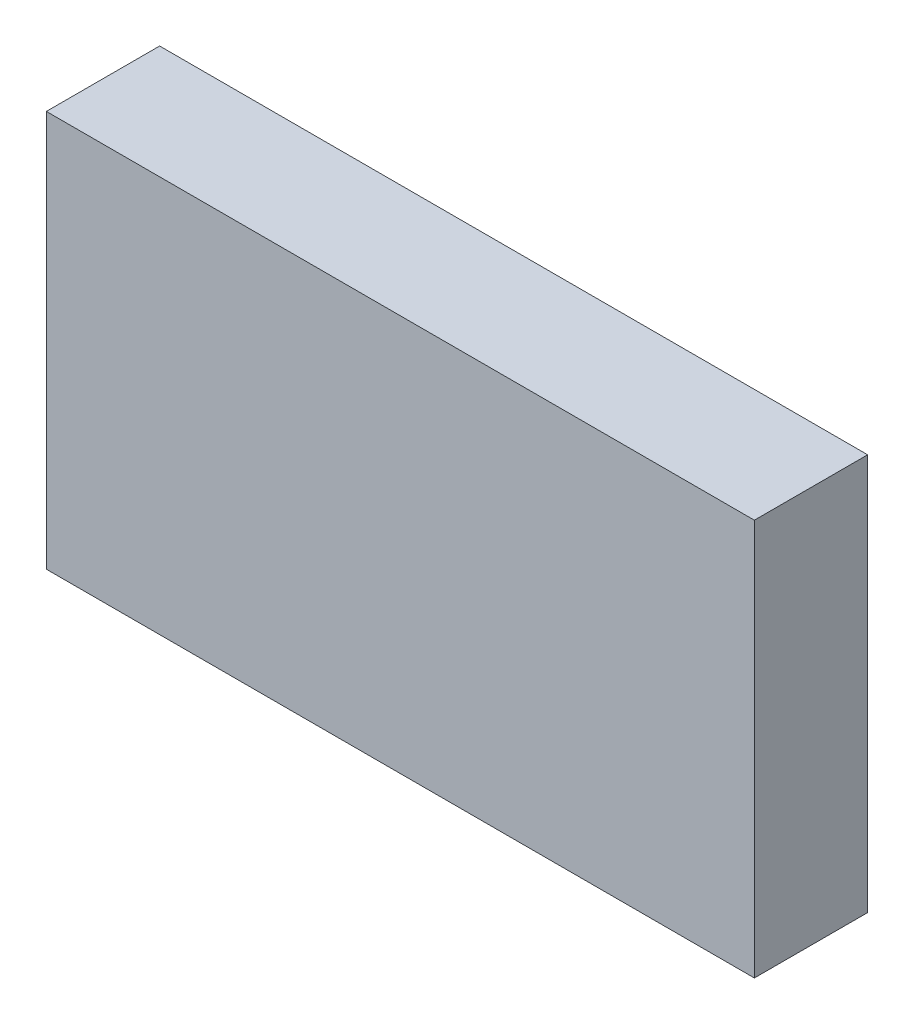
SolidWorks part; units mm, degrees
other "Target"
ref_plane "Front Plane" through (0, 0, 0) normal (0, 0, 1) x (1, 0, 0)
ref_plane "Top Plane" through (0, 0, 0) normal (0, 1, 0) x (1, 0, 0)
ref_plane "Right Plane" through (0, 0, 0) normal (1, 0, 0) x (0, 0, -1)
sketch "Sketch1" plane through (0, 0, 0) normal (0, 0, 1) x (1, 0, 0)
  line L1 (-76.2, -41.275) -> (76.2, -41.275)
  line L2 (-76.2, -41.275) -> (-76.2, 41.275)
  line L3 (-76.2, 41.275) -> (76.2, 41.275)
  line L4 (76.2, -41.275) -> (76.2, 41.275)
  line L5 (-76.2, -41.275) -> (76.2, 41.275) construction
  line L6 (-76.2, 41.275) -> (76.2, -41.275) construction
  point P0 (0, 0)
  dimension "D1" = 152.4
  dimension "D2" = 82.55
extrude "Extrude1" add sketch "Sketch1" along normal blind 19.05
sketch "Sketch2" plane through (0, 0, 19.05) normal (0, 0, 1) x (1, 0, 0)
  line L0 (76.2, 41.275) -> (-76.2, 41.275) construction
  line L1 (71.12, 36.195) -> (-60.325, 36.195)
  line L2 (71.12, 36.195) -> (71.12, -36.195)
  line L3 (71.12, -36.195) -> (-60.325, -36.195)
  line L4 (-60.325, 36.195) -> (-60.325, -36.195)
  line L5 (76.2, -41.275) -> (76.2, 41.275) construction
  line L6 (-76.2, -41.275) -> (76.2, -41.275) construction
  line L7 (-76.2, 41.275) -> (-76.2, -41.275) construction
  dimension "D1" = 5.08
  dimension "D2" = 5.08
  dimension "D3" = 5.08
  dimension "D4" = 15.875
extrude "Extrude2" cut sketch "Sketch2" against normal blind 12.7
fillet "Fillet1" radius 2.54 4 edges at (76.2, 41.275, 9.525) (76.2, -41.275, 9.525) (-76.2, -41.275, 9.525) (-76.2, 41.275, 9.525)
fillet "Fillet2" radius 5.08 4 edges at (71.12, 36.195, 12.7) (71.12, -36.195, 12.7) (-60.325, -36.195, 12.7) (-60.325, 36.195, 12.7)
sketch "Sketch3" plane through (0, 0, 19.05) normal (0, 0, 1) x (1, 0, 0)
  line L0 (-60.325, 31.115) -> (-60.325, -31.115) construction
  line L1 (-60.325, 22.225) -> (-71.12, 22.225)
  line L2 (-60.325, 22.225) -> (-60.325, -22.225)
  line L3 (-60.325, -22.225) -> (-71.12, -22.225)
  line L4 (-71.12, 22.225) -> (-71.12, -22.225)
  line L5 (-76.2, 0) -> (-39.8862, 0) construction
  line L6 (-76.2, 38.735) -> (-76.2, -38.735) construction
  dimension "D1" = 5.08
  dimension "D2" = 44.45
extrude "Extrude3" cut sketch "Sketch3" against normal blind 6.35
fillet "Fillet3" radius 5.08 2 edges at (-71.12, 22.225, 15.875) (-71.12, -22.225, 15.875)
sketch "Sketch4" plane through (0, 0, 19.05) normal (0, 0, 1) x (1, 0, 0)
  line L1 (-79.375, -44.45) -> (79.375, -44.45)
  line L2 (-79.375, -44.45) -> (-79.375, 44.45)
  line L3 (-79.375, 44.45) -> (79.375, 44.45)
  line L4 (79.375, -44.45) -> (79.375, 44.45)
  line L5 (-79.375, -44.45) -> (79.375, 44.45) construction
  line L6 (-79.375, 44.45) -> (79.375, -44.45) construction
  point P0 (0, 0)
  dimension "D1" = 158.75
  dimension "D2" = 88.9
extrude "Stock" add sketch "Sketch4" against normal blind 25.4 separate body
